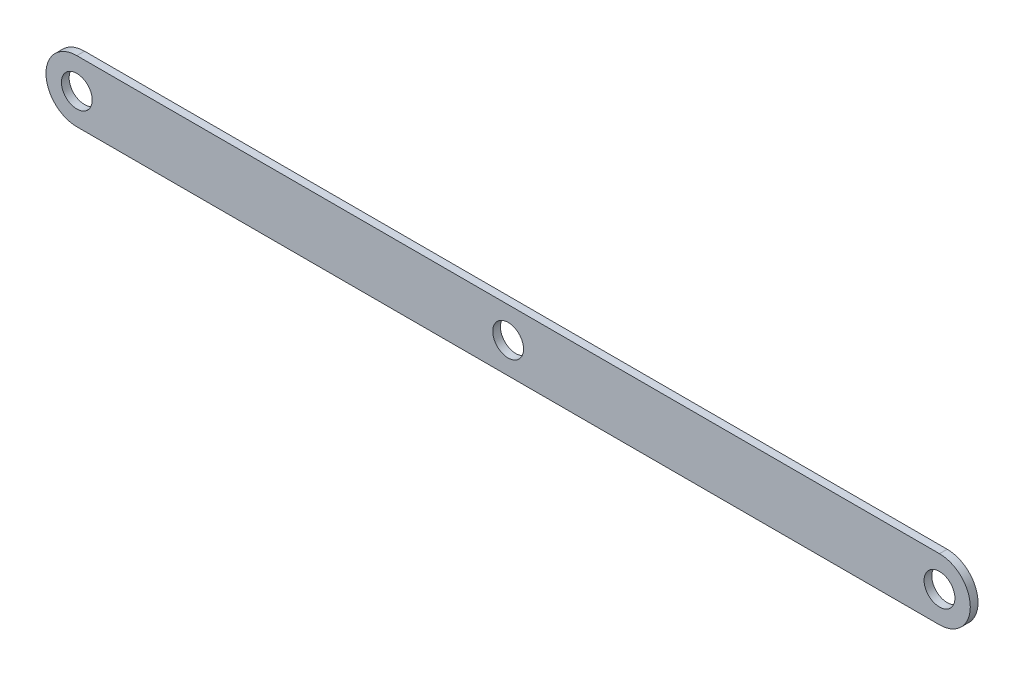
SolidWorks part; units mm, degrees
ref_plane "Front Plane" through (0, 0, 0) normal (0, 0, 1) x (1, 0, 0)
ref_plane "Top Plane" through (0, 0, 0) normal (0, 1, 0) x (1, 0, 0)
ref_plane "Right Plane" through (0, 0, 0) normal (1, 0, 0) x (0, 0, -1)
sketch "Sketch1" plane through (0, 0, 0) normal (0, 0, 1) x (1, 0, 0)
  line L0 (177.8, 0) -> (-177.8, 0) construction
  line L1 (177.8, -12.7) -> (-177.8, -12.7)
  line L2 (177.8, 12.7) -> (-177.8, 12.7)
  arc A0 (177.8, -12.7) -> (177.8, 12.7) centre (177.8, 0) ccw
  arc A1 (-177.8, 12.7) -> (-177.8, -12.7) centre (-177.8, 0) ccw
  circle A2 centre (-177.8, 0) radius 6.35
  circle A3 centre (0, 0) radius 6.35
  circle A4 centre (177.8, 0) radius 6.35
  point P2 (0, 0)
  dimension "D3" = 12.7
  dimension "D1" = 355.6
  dimension "D2" = 25.4
extrude "Boss-Extrude1" add sketch "Sketch1" along normal blind 3.175
